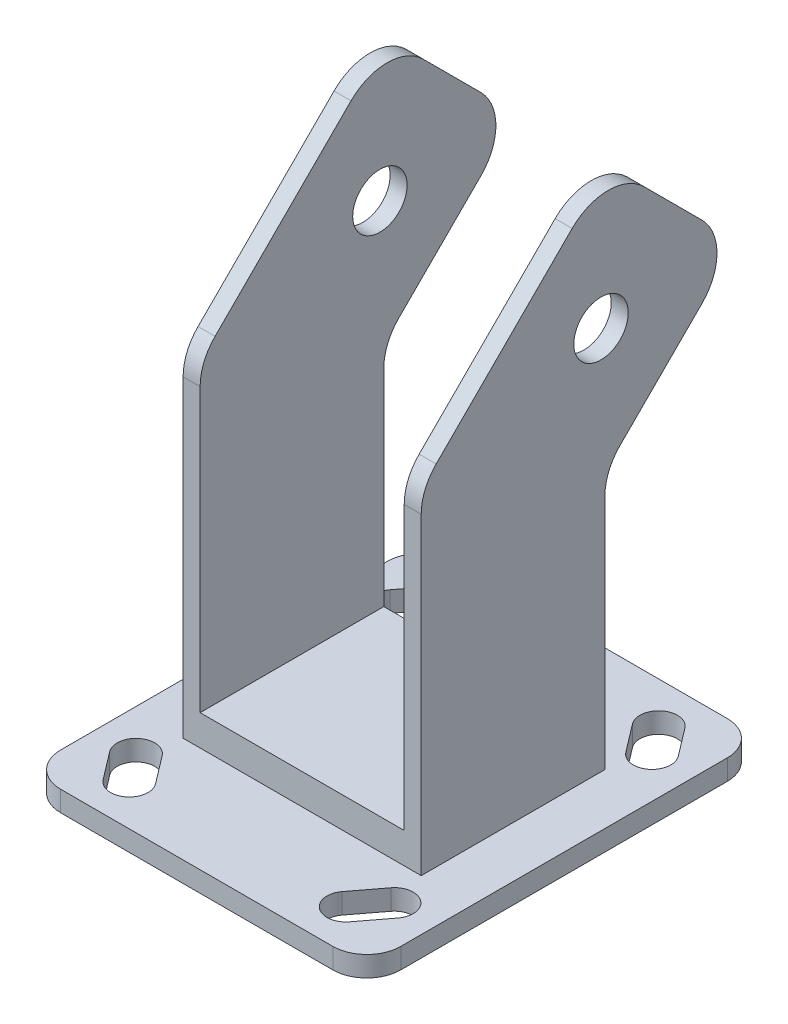
SolidWorks part; units mm, degrees
ref_plane "Front Plane" through (0, 0, 0) normal (0, 0, 1) x (1, 0, 0)
ref_plane "Top Plane" through (0, 0, 0) normal (0, 1, 0) x (1, 0, 0)
ref_plane "Right Plane" through (0, 0, 0) normal (1, 0, 0) x (0, 0, -1)
sketch "Sketch1" plane through (0, 0, 0) normal (0, 1, 0) x (1, 0, 0)
  line L5 (50, 58) -> (-50, 58)
  line L6 (50, 58) -> (50, -58)
  line L7 (50, -58) -> (-50, -58)
  line L8 (-50, 58) -> (-50, -58)
  line L9 (50, 58) -> (-50, -58) construction
  line L10 (50, -58) -> (-50, 58) construction
  point P0 (0, 0)
extrude "Boss-Extrude1" add sketch "Sketch1" along normal blind 6
fillet "Fillet1" radius 10 4 edges at (-50, 3, -58) (50, 3, -58) (50, 3, 58) (-50, 3, 58)
sketch "Sketch2" plane through (0, 6, 0) normal (0, 1, 0) x (1, 0, 0)
  line L7 (-50, 48) -> (-50, -48) construction
  line L10 (40, 58) -> (-40, 58) construction
  line L11 (-31.8128, 46) -> (-38, 37.8683) construction
  line L12 (-36.1899, 49.3304) -> (-42.3771, 41.1986)
  line L13 (-27.4358, 42.6696) -> (-33.6229, 34.5379)
  line L14 (31.8128, 46) -> (38, 37.8683) construction
  line L17 (36.1899, 49.3304) -> (42.3771, 41.1986)
  line L20 (27.4358, 42.6696) -> (33.6229, 34.5379)
  line L21 (-31.8128, -46) -> (-38, -37.8683) construction
  line L22 (-36.1899, -49.3304) -> (-42.3771, -41.1986)
  line L23 (-27.4358, -42.6696) -> (-33.6229, -34.5379)
  line L24 (31.8128, -46) -> (38, -37.8683) construction
  line L25 (36.1899, -49.3304) -> (42.3771, -41.1986)
  line L26 (27.4358, -42.6696) -> (33.6229, -34.5379)
  arc A2 (-36.1899, 49.3304) -> (-27.4358, 42.6696) centre (-31.8128, 46) cw
  arc A3 (-33.6229, 34.5379) -> (-42.3771, 41.1986) centre (-38, 37.8683) cw
  arc A8 (36.1899, 49.3304) -> (27.4358, 42.6696) centre (31.8128, 46) ccw
  arc A9 (33.6229, 34.5379) -> (42.3771, 41.1986) centre (38, 37.8683) ccw
  arc A10 (-36.1899, -49.3304) -> (-27.4358, -42.6696) centre (-31.8128, -46) ccw
  arc A11 (-33.6229, -34.5379) -> (-42.3771, -41.1986) centre (-38, -37.8683) ccw
  arc A12 (36.1899, -49.3304) -> (27.4358, -42.6696) centre (31.8128, -46) cw
  arc A13 (33.6229, -34.5379) -> (42.3771, -41.1986) centre (38, -37.8683) cw
  point P4 (34.9064, 41.9341)
  point P17 (-34.9064, 41.9341)
  point P22 (-34.9064, -41.9341)
  point P29 (34.9064, -41.9341)
  dimension "D3" = 12
  dimension "D4" = 12
extrude "Cut-Extrude1" cut sketch "Sketch2" against normal blind 6
sketch "Sketch3" plane through (0, 6, 0) normal (0, 1, 0) x (1, 0, 0)
  line L1 (-35, 27) -> (35, 27)
  line L2 (-35, 27) -> (-35, -27)
  line L3 (-35, -27) -> (35, -27)
  line L4 (35, 27) -> (35, -27)
  line L5 (-35, 27) -> (35, -27) construction
  line L6 (-35, -27) -> (35, 27) construction
  point P0 (0, 0)
extrude "Boss-Extrude2" add sketch "Sketch3" along normal blind 9
sketch "Sketch5" plane through (-35, 0, 0) normal (-1, 0, 0) x (0, 0, 1)
  line L0 (-27, 15) -> (27, 15)
  line L1 (-27, 15) -> (-27, 75.6468)
  line L3 (27, 98.0143) -> (27, 15)
  line L4 (-31.3934, 86.2534) -> (-55.553, 110.413)
  line L7 (-55.553, 131.6262) -> (-38.5824, 148.5967)
  line L8 (-17.3692, 148.5967) -> (22.6066, 108.6209)
  arc A0 (22.6066, 108.6209) -> (27, 98.0143) centre (12, 98.0143) cw
  arc A1 (-27, 75.6468) -> (-31.3934, 86.2534) centre (-42, 75.6468) ccw
  arc A2 (-38.5824, 148.5967) -> (-17.3692, 148.5967) centre (-27.9758, 137.9901) cw
  arc A3 (-55.553, 110.413) -> (-55.553, 131.6262) centre (-44.9464, 121.0196) cw
  circle A4 centre (-25.8545, 118.8983) radius 8
  dimension "D1" = 15
  dimension "D2" = 15
extrude "Boss-Extrude3" add sketch "Sketch5" against normal blind 5
mirror "Mirror1" about plane through (0, 0, 0) normal (1, 0, 0) of "Boss-Extrude3"
